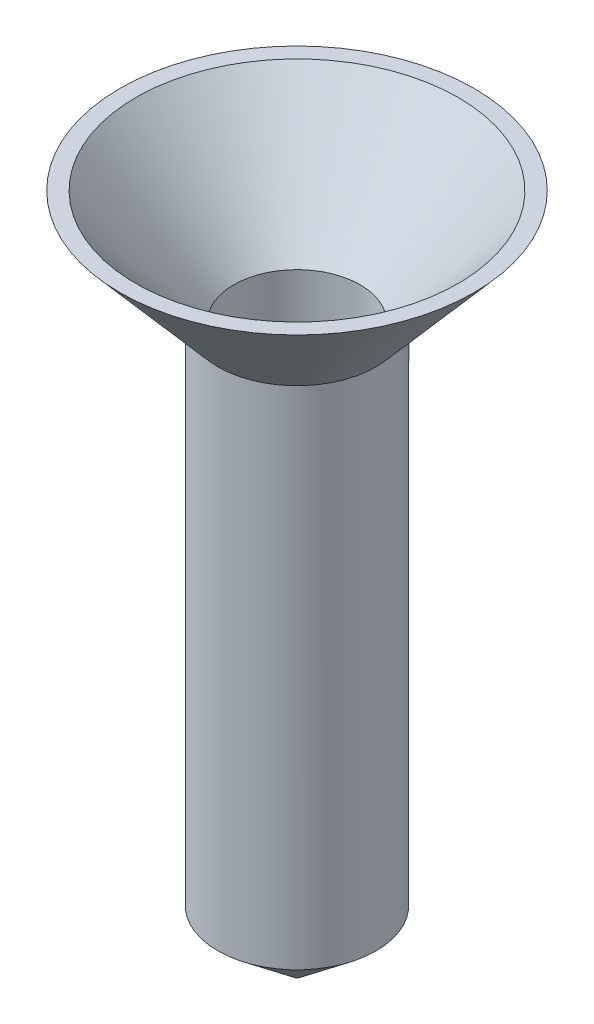
SolidWorks part; units mm, degrees
ref_plane "Front Plane" through (0, 0, 0) normal (0, 0, 1) x (1, 0, 0)
ref_plane "Top Plane" through (0, 0, 0) normal (0, 1, 0) x (1, 0, 0)
ref_plane "Right Plane" through (0, 0, 0) normal (1, 0, 0) x (0, 0, -1)
sketch "Sketch2" plane through (0, 0, 0) normal (0, 1, 0) x (1, 0, 0)
  circle A0 centre (0, 0) radius 31.75
  circle A1 centre (0, 0) radius 25.4
  dimension "D1" = 63.5
  dimension "D2" = 50.8
extrude "Boss-Extrude1" add sketch "Sketch2" against normal blind 254
sketch "Sketch4" plane through (0, 0, 0) normal (1, 0, 0) x (0, 0, -1)
  line L0 (31.75, 0) -> (71.0931, 45.4884)
  line L1 (25.4, 0) -> (64.7431, 45.4884)
  line L2 (64.7431, 45.4884) -> (71.0931, 45.4884)
  line L3 (0, 0) -> (0, 23.7945) construction
  line L4 (25.4, 0) -> (31.75, 0) construction
  line L5 (31.75, 0) -> (25.4, 0)
revolve "Revolve1" add sketch "Sketch4" angle 360 about L3
sketch "Sketch5" plane through (0, -254, 0) normal (0, -1, 0) x (1, 0, 0)
  circle A0 centre (0, 0) radius 46.8059
extrude "Cut-Extrude1" cut sketch "Sketch5" against normal blind 50.8
sketch "Sketch6" plane through (0, 0, 0) normal (1, 0, 0) x (0, 0, -1)
  line L0 (-31.75, -203.2) -> (-25.4, -203.2)
  line L4 (-1.3517, -227.5186) -> (-31.75, -203.2)
  line L5 (-25.4, -203.2) -> (-0.6759, -225.2269)
  line L9 (-1.3517, -227.5186) -> (-0.6759, -225.2269)
revolve "Revolve2" add sketch "Sketch6" angle 360 about axis through (0, -254, 0) along (0, 1, 0)
